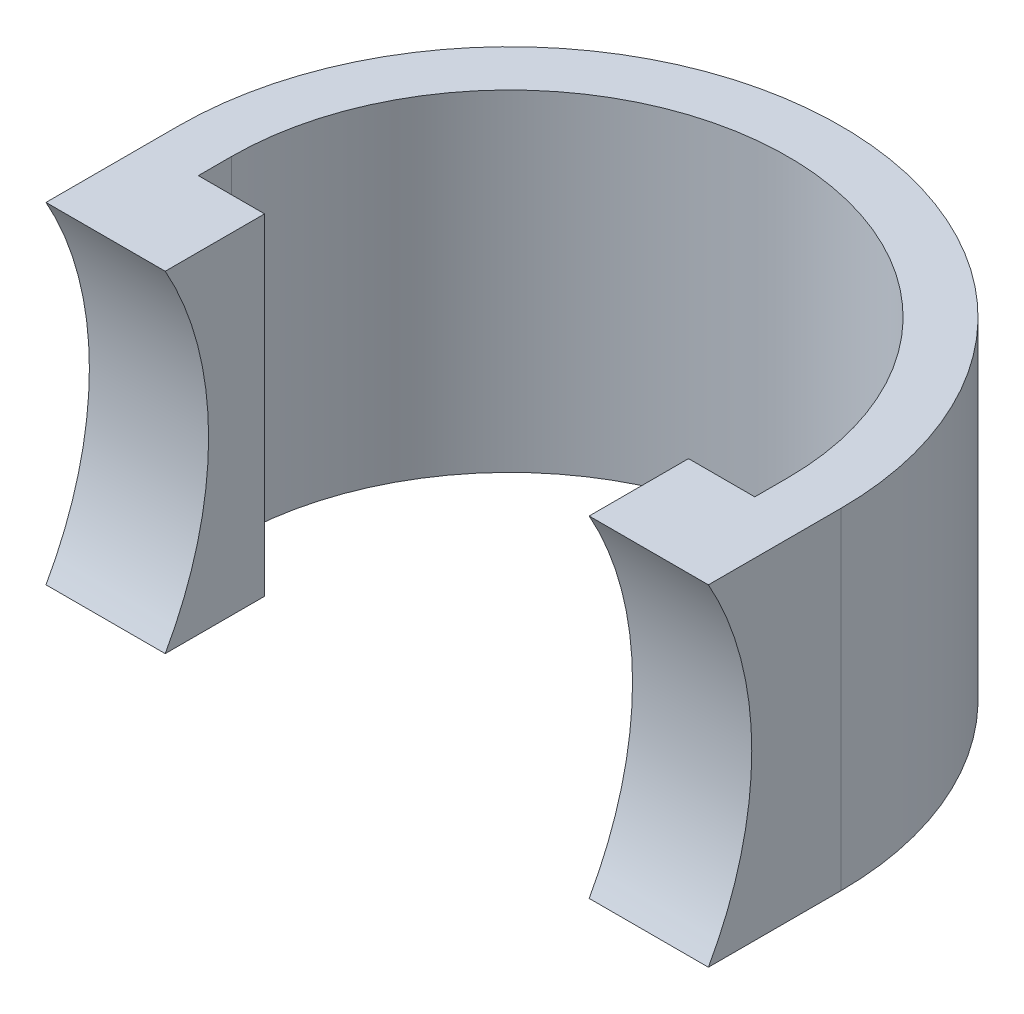
SolidWorks part; units mm, degrees
material "PET"
ref_plane "Front Plane" through (0, 0, 0) normal (0, 0, 1) x (1, 0, 0)
ref_plane "Top Plane" through (0, 0, 0) normal (0, 1, 0) x (1, 0, 0)
ref_plane "Right Plane" through (0, 0, 0) normal (1, 0, 0) x (0, 0, -1)
sketch "Sketch1" plane through (0, 0, 0) normal (0, 0, 1) x (1, 0, 0)
  line L1 (-35.0731, 14.8225) -> (64.9269, 14.8225)
  line L2 (-35.0731, 14.8225) -> (-35.0731, -35.1775)
  line L3 (-35.0731, -35.1775) -> (64.9269, -35.1775)
  line L4 (64.9269, 14.8225) -> (64.9269, -35.1775)
  dimension "D1" = 100
  dimension "D2" = 50
extrude "Boss-Extrude1" add sketch "Sketch1" along normal blind 100
sketch "Sketch2" plane through (-35.0731, 0, 0) normal (-1, 0, 0) x (0, 0, 1)
  line L1 (100, -10.1775) -> (144.4522, -10.1775) construction
  line L2 (100, 14.8225) -> (100, -35.1775) construction
  circle A0 centre (144.4522, -10.1775) radius 51
  dimension "D1" = 102
extrude "Cut-Extrude1" cut sketch "Sketch2" against normal blind 100
sketch "Sketch3" plane through (0, -35.1775, 0) normal (0, -1, 0) x (1, 0, 0)
  line L0 (14.9269, 100) -> (14.9269, 0) construction
  line L1 (-35.0731, 100) -> (64.9269, 100) construction
  line L2 (-35.0731, 0) -> (64.9269, 0) construction
  line L3 (-35.0731, 80) -> (-35.0731, 0)
  line L4 (-35.0731, 0) -> (64.9269, 0)
  line L5 (64.9269, 0) -> (64.9269, 80)
  line L6 (-27.0731, 85) -> (-17.0731, 85)
  line L7 (-17.0731, 85) -> (-17.0731, 100)
  line L8 (-17.0731, 100) -> (46.9269, 100)
  line L9 (46.9269, 100) -> (46.9269, 85)
  line L10 (46.9269, 85) -> (56.9269, 85)
  line L11 (-27.0731, 80) -> (-27.0731, 85)
  line L12 (56.9269, 80) -> (56.9269, 85)
  arc A0 (-35.0731, 80) -> (64.9269, 80) centre (14.9269, 80) ccw
  arc A1 (-27.0731, 80) -> (56.9269, 80) centre (14.9269, 80) ccw
  dimension "D2" = 8
  dimension "D1" = 20
  dimension "D3" = 10
  dimension "D4" = 10
  dimension "D5" = 15
extrude "Cut-Extrude2" cut sketch "Sketch3" against normal blind 100
